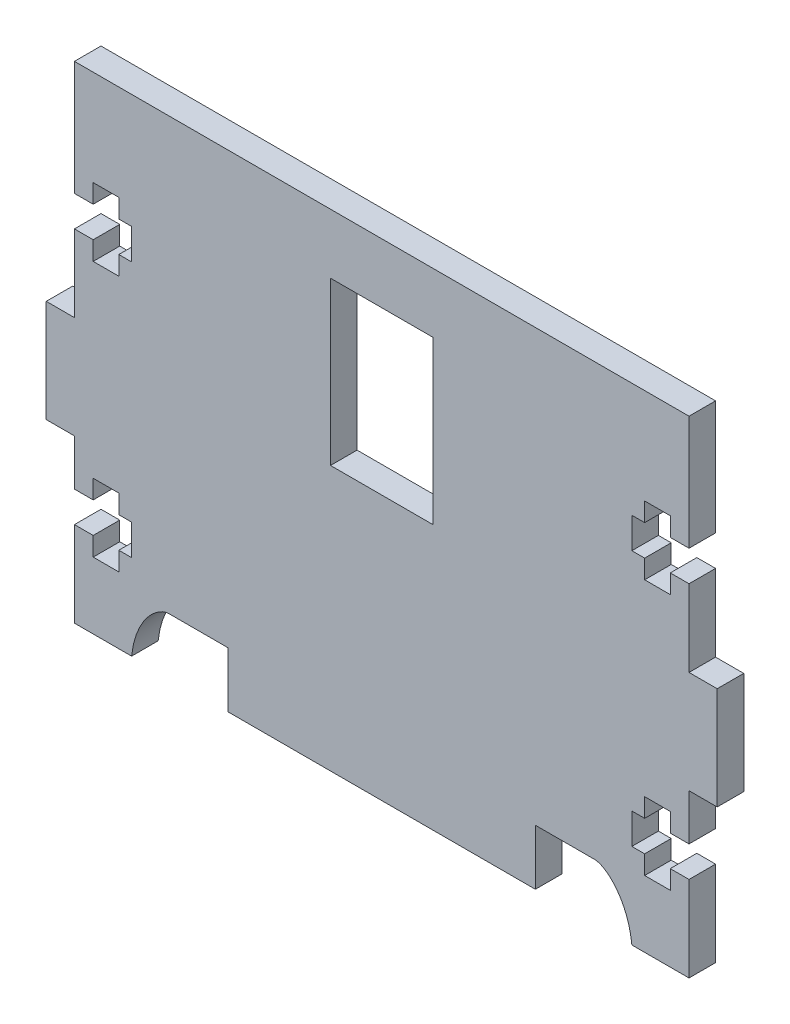
SolidWorks part; units mm, degrees
ref_plane "정면" through (0, 0, 0) normal (0, 0, 1) x (1, 0, 0)
ref_plane "윗면" through (0, 0, 0) normal (0, 1, 0) x (1, 0, 0)
ref_plane "우측면" through (0, 0, 0) normal (1, 0, 0) x (0, 0, -1)
sketch "Sketch2" plane through (0, 0, 0) normal (0, 0, 1) x (1, 0, 0)
  line L0 (12.8311, 10.1302) -> (18.8311, 10.1302) construction
  line L1 (37.8311, 10.1302) -> (37.8311, -39.8698) construction
  line L2 (37.8311, -39.8698) -> (-5.1689, -39.8698) construction
  line L3 (-12.1689, -33.3698) -> (-12.1689, 10.1302) construction
  line L4 (-5.1689, -39.8698) -> (-5.1689, -33.3698)
  line L5 (18.8311, 10.1302) -> (18.8311, -8.8698)
  line L6 (18.8311, -8.8698) -> (6.8311, -8.8698)
  line L7 (6.8311, -8.8698) -> (6.8311, 10.1302)
  line L8 (-23.1689, 10.1302) -> (-23.1689, 17.1302)
  line L9 (-23.1689, 17.1302) -> (48.8311, 17.1302)
  line L10 (48.8311, 17.1302) -> (48.8311, 10.1302)
  line L11 (30.8311, -39.8698) -> (30.8311, -33.3698)
  line L12 (30.8311, -33.3698) -> (37.8311, -33.3698)
  line L13 (42.1331, -39.8698) -> (48.8311, -39.8698)
  line L14 (42.1331, -29.8698) -> (42.1331, -39.8698) construction
  line L15 (-5.1689, -33.3698) -> (-12.1689, -33.3698)
  line L16 (-5.1689, -39.8698) -> (30.8311, -39.8698)
  line L17 (46.642, 3.7302) -> (46.6331, 3.7302)
  line L18 (46.6331, 3.7302) -> (46.6331, 5.9302)
  line L19 (46.6331, 5.9302) -> (43.6331, 5.9302)
  line L20 (43.6331, 5.9302) -> (43.6331, 3.7302)
  line L21 (43.6331, -2.0698) -> (43.6331, 0.1302)
  line L22 (46.6331, -2.0698) -> (43.6331, -2.0698)
  line L23 (46.6331, 0.1302) -> (46.6331, -2.0698)
  line L24 (46.642, 0.1302) -> (46.6331, 0.1302)
  line L25 (43.6331, 3.7302) -> (42.1331, 3.7302)
  line L26 (-23.1689, -8.8698) -> (-23.1689, 0.1302)
  line L27 (42.1331, 0.1302) -> (42.1331, 3.7302)
  line L28 (43.6331, 0.1302) -> (42.1331, 0.1302)
  line L29 (46.642, 0.1302) -> (48.8311, 0.1302)
  line L30 (46.642, 3.7302) -> (48.8311, 3.7302)
  line L31 (-20.9709, -29.8698) -> (-23.1689, -29.8698)
  line L32 (-23.1689, -39.8698) -> (-16.4709, -39.8698)
  line L33 (-23.1689, -39.8698) -> (-23.1689, -33.4698)
  line L34 (6.8311, 10.1302) -> (18.8311, 10.1302)
  line L35 (48.8311, -39.8698) -> (48.8311, -29.8698)
  line L36 (-16.4709, 1.9302) -> (-34.4896, 1.9302) construction
  line L37 (-23.1689, -39.8698) -> (-16.4709, -39.8698) construction
  line L38 (-20.9709, -29.8698) -> (-20.9709, -32.0698)
  line L39 (-20.9709, -32.0698) -> (-17.9709, -32.0698)
  line L40 (-23.1689, -39.8698) -> (-23.1689, -29.8698) construction
  line L41 (-26.4709, -14.8698) -> (48.8311, -14.8698) construction
  line L42 (-17.9709, -32.0698) -> (-17.9709, -29.8698)
  line L43 (-17.9709, -29.8698) -> (-16.4709, -29.8698)
  line L44 (-16.4709, -26.2698) -> (-16.4709, -29.8698)
  line L45 (-17.9709, -26.2698) -> (-16.4709, -26.2698)
  line L46 (-17.9709, -24.0698) -> (-17.9709, -26.2698)
  line L47 (-20.9709, -24.0698) -> (-17.9709, -24.0698)
  line L48 (-20.9709, -26.2698) -> (-20.9709, -24.0698)
  line L49 (-20.9709, -26.2698) -> (-23.1689, -26.2698)
  line L50 (48.8311, 0.1302) -> (48.8311, -3.4698)
  line L51 (-23.1689, -29.8698) -> (-23.1689, -33.4698)
  line L52 (46.6331, -26.2698) -> (48.8311, -26.2698)
  line L53 (12.8311, 10.1302) -> (12.8311, -39.8698) construction
  line L54 (48.8311, -6.8698) -> (48.8311, -8.8698)
  line L55 (48.8311, -20.8698) -> (52.1331, -20.8698)
  line L56 (52.1331, -20.8698) -> (52.1331, -8.8698)
  line L57 (52.1331, -8.8698) -> (48.8311, -8.8698)
  line L58 (46.6331, -26.2698) -> (46.6331, -24.0698)
  line L59 (46.6331, -24.0698) -> (43.6331, -24.0698)
  line L60 (43.6331, -24.0698) -> (43.6331, -26.2698)
  line L61 (43.6331, -26.2698) -> (42.1331, -26.2698)
  line L62 (42.1331, -26.2698) -> (42.1331, -29.8698)
  line L63 (43.6331, -29.8698) -> (42.1331, -29.8698)
  line L64 (43.6331, -32.0698) -> (43.6331, -29.8698)
  line L65 (46.6331, -32.0698) -> (43.6331, -32.0698)
  line L66 (46.6331, -29.8698) -> (46.6331, -32.0698)
  line L67 (46.6331, -29.8698) -> (48.8311, -29.8698)
  line L68 (-20.9798, 3.7302) -> (-23.1689, 3.7302)
  line L69 (-20.9798, 0.1302) -> (-23.1689, 0.1302)
  line L70 (-17.9709, 0.1302) -> (-16.4709, 0.1302)
  line L71 (-16.4709, 0.1302) -> (-16.4709, 3.7302)
  line L72 (-17.9709, 3.7302) -> (-16.4709, 3.7302)
  line L73 (-20.9798, 0.1302) -> (-20.9709, 0.1302)
  line L74 (-20.9709, 0.1302) -> (-20.9709, -2.0698)
  line L75 (-20.9709, -2.0698) -> (-17.9709, -2.0698)
  line L76 (-17.9709, -2.0698) -> (-17.9709, 0.1302)
  line L77 (-17.9709, 5.9302) -> (-17.9709, 3.7302)
  line L78 (-20.9709, 5.9302) -> (-17.9709, 5.9302)
  line L79 (-20.9709, 3.7302) -> (-20.9709, 5.9302)
  line L80 (-20.9798, 3.7302) -> (-20.9709, 3.7302)
  line L81 (48.8311, 3.7302) -> (48.8311, 10.1302)
  line L82 (48.8311, -26.2698) -> (48.8311, -22.8698)
  line L83 (-23.1689, 3.7302) -> (-23.1689, 10.1302)
  line L84 (48.8311, -6.8698) -> (48.8311, -3.4698)
  line L85 (48.8311, -20.8698) -> (48.8311, -22.8698)
  line L86 (-23.1689, -20.8698) -> (-26.4709, -20.8698)
  line L87 (-26.4709, -20.8698) -> (-26.4709, -8.8698)
  line L88 (-26.4709, -8.8698) -> (-23.1689, -8.8698)
  line L89 (-23.1689, -20.8698) -> (-23.1689, -26.2698)
  spline S0 degree 3 poles (37.8311, -33.3698) (39.2142, -33.4599) (41.7018, -35.6951) (42.1331, -39.8698) knots 0 0 0 0 1 1 1 1
  spline S1 degree 3 poles (-12.1689, -33.3698) (-13.5521, -33.4599) (-16.0396, -35.6951) (-16.4709, -39.8698) knots 0 0 0 0 1 1 1 1
  dimension "D1" = 12
  dimension "D2" = 10.8
  dimension "D3" = 78.604
  dimension "D4" = 57
extrude "Boss-Extrude1" add sketch "Sketch2" along normal blind 3.1115
